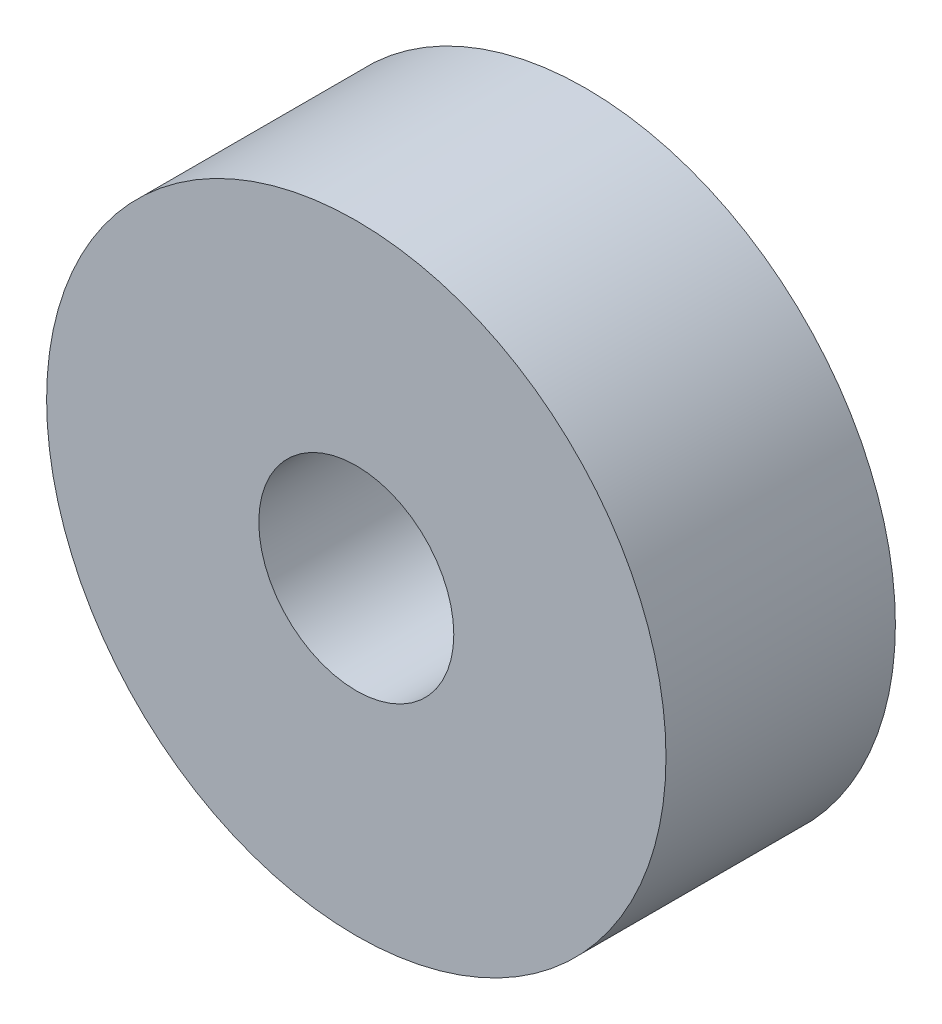
SolidWorks part; units mm, degrees
ref_plane "Front Plane" through (0, 0, 0) normal (0, 0, 1) x (1, 0, 0)
ref_plane "Top Plane" through (0, 0, 0) normal (0, 1, 0) x (1, 0, 0)
ref_plane "Right Plane" through (0, 0, 0) normal (1, 0, 0) x (0, 0, -1)
sketch "Sketch1" plane through (0, 0, 0) normal (0, 0, 1) x (1, 0, 0)
  circle A0 centre (0, 0) radius 27
  dimension "D1" = 54
extrude "Boss-Extrude1" add sketch "Sketch1" along normal blind 20
sketch "Sketch2" plane through (0, 0, 20) normal (0, 0, 1) x (1, 0, 0)
  circle A0 centre (0, 0) radius 8.5
  dimension "D1" = 17
extrude "Cut-Extrude1" cut sketch "Sketch2" against normal up to next
